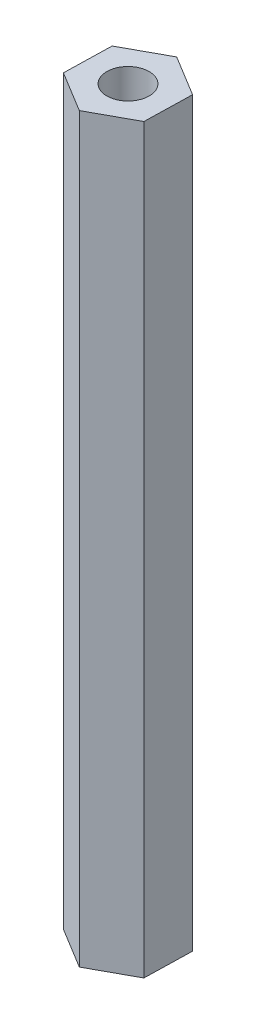
SolidWorks part; units mm, degrees
material "3003 Alloy"
ref_plane "Front Plane" through (0, 0, 0) normal (0, 0, 1) x (1, 0, 0)
ref_plane "Top Plane" through (0, 0, 0) normal (0, 1, 0) x (1, 0, 0)
ref_plane "Right Plane" through (0, 0, 0) normal (1, 0, 0) x (0, 0, -1)
sketch "Sketch1" plane through (0, 0, 0) normal (0, 1, 0) x (1, 0, 0)
  line L1 (6.4344, 3.5159) -> (0.1723, 7.3303)
  line L2 (0.1723, 7.3303) -> (-6.2621, 3.8144)
  line L3 (-6.2621, 3.8144) -> (-6.4344, -3.5159)
  line L4 (-6.4344, -3.5159) -> (-0.1723, -7.3303)
  line L5 (-0.1723, -7.3303) -> (6.2621, -3.8144)
  line L6 (6.2621, -3.8144) -> (6.4344, 3.5159)
  circle A0 centre (0, 0) radius 6.35 construction
  dimension "D1" = 12.7
extrude "Boss-Extrude1" add sketch "Sketch1" along normal mid plane 114.3
sketch "Sketch2" plane through (0, 57.15, 0) normal (0, 1, 0) x (1, 0, 0)
  circle A0 centre (0, 0) radius 3.2639
  dimension "D1" = 6.5278
extrude "Cut-Extrude1" cut sketch "Sketch2" against normal blind 12.7
mirror "Mirror1" about plane through (0, 0, 0) normal (0, 1, 0) of "Cut-Extrude1"
